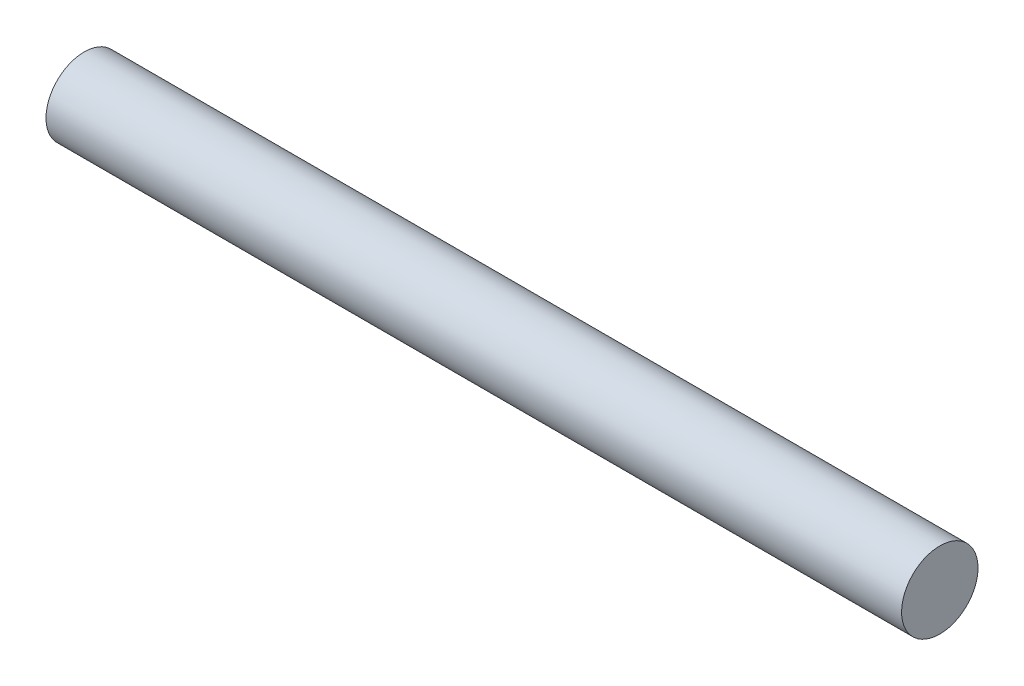
SolidWorks part; units mm, degrees
ref_plane "Front Plane" through (0, 0, 0) normal (0, 0, 1) x (1, 0, 0)
ref_plane "Top Plane" through (0, 0, 0) normal (0, 1, 0) x (1, 0, 0)
ref_plane "Right Plane" through (0, 0, 0) normal (1, 0, 0) x (0, 0, -1)
sketch "Sketch1" plane through (0, 0, 0) normal (1, 0, 0) x (0, 0, -1)
  circle A0 centre (0, 0) radius 6.35
  dimension "D1" = 12.7
extrude "Boss-Extrude1" add sketch "Sketch1" along normal offset from surface 1.5875 and the other way offset from surface (71.0875 mm away) 1.5875
sketch "Sketch3" plane through (71.0875, 0, 0) normal (1, 0, 0) x (0, 0, -1)
  circle A1 centre (0, 0) radius 6.35
  circle A2 centre (0, 0) radius 6.35
  dimension "D1" = 0
extrude "Boss-Extrude2" [suppressed] add sketch "Sketch3" along normal blind 3.175
sketch "Sketch2" [suppressed] plane through (0, 0, 0) normal (0, 0, 1) x (1, 0, 0)
  line L0 (0, 0) -> (72.675, 0) construction
  line L1 (70.6684, 5.0292) -> (69.5, 5.0292)
  line L2 (70.6684, 5.0292) -> (70.6684, 6.35)
  line L3 (70.6684, 6.35) -> (69.5, 6.35)
  line L4 (69.5, 5.0292) -> (69.5, 6.35)
  line L6 (72.675, 6.35) -> (-69.5, 6.35) construction
  line L8 (72.675, -6.35) -> (72.675, 6.35) construction
  dimension "D1" = 1.1684
  dimension "D2" = 10.0584
  dimension "D3" = 3.175
revolve "Cut-Revolve1" [suppressed] cut sketch "Sketch2" angle 360 about L0
hole_wizard "1/4-20 Tapped Hole1" [suppressed] positions "Sketch8" profile "Sketch10" tap size "1/4-20" standard "ANSI Inch"
sketch "Sketch8" plane through (-69.5, 0, 0) normal (-1, 0, 0) x (0, 0, 1)
  point P0 (0, 0)
sketch "Sketch10" plane through (-69.5, 0, 0) normal (0, 1, 0) x (0, 0, 1)
  line L0 (0, 0) -> (0, 18.0438)
  line L1 (0, 18.0438) -> (2.5527, 16.51)
  line L2 (2.5527, 16.51) -> (2.5527, 0)
  line L5 (2.5527, 0) -> (0, 0)
  line L10 (0, 18.0438) -> (-2.5527, 16.51) construction
  line L11 (0, -6.35) -> (0, 107.95) construction
  dimension "Tap Drill Dia." = 5.1054
  dimension "Tap Drill Depth" = 16.51
  dimension "Drill Angle" = 118
cosmetic thread "Hole Thread1" [suppressed] parameters "D1"=12.7, "D2"=6.35
equation "\"ShaftDia\"=0.5"
equation "\"D1\"= \"YokeWidth\""
equation "\"EncoderWidth\"=0.125"
equation "\"D1@Boss-Extrude2\"=\"EncoderWidth\""
equation "\"D3@Sketch2\"=\"EncoderWidth\""
